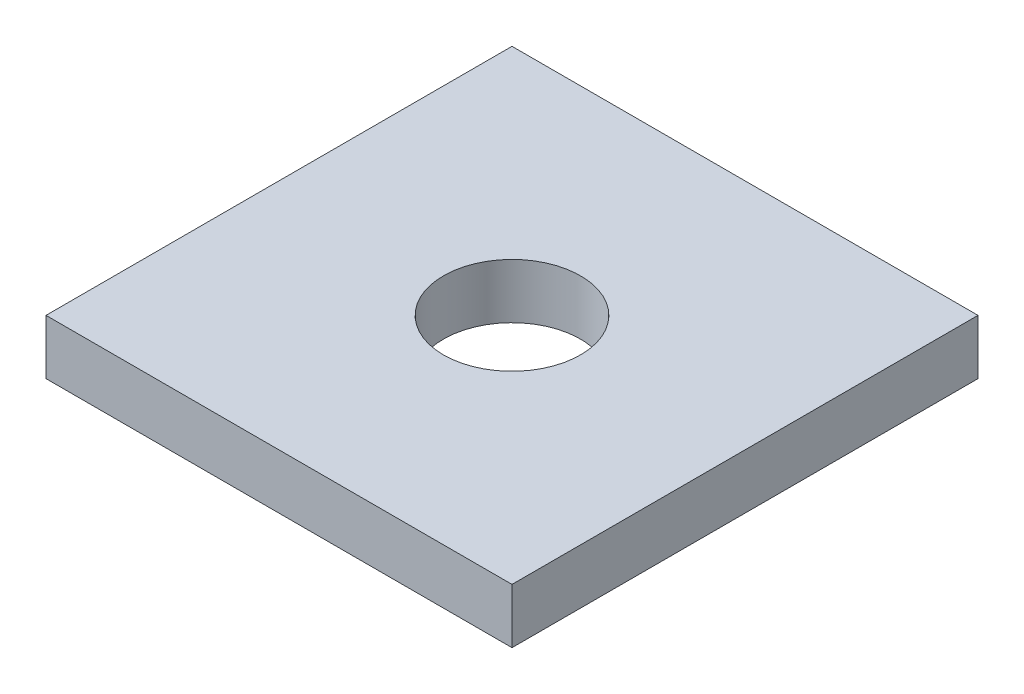
SolidWorks part; units mm, degrees
ref_plane "Front Plane" through (0, 0, 0) normal (0, 0, 1) x (1, 0, 0)
ref_plane "Top Plane" through (0, 0, 0) normal (0, 1, 0) x (1, 0, 0)
ref_plane "Right Plane" through (0, 0, 0) normal (1, 0, 0) x (0, 0, -1)
sketch "Sketch1" plane through (0, 0, 0) normal (0, 1, 0) x (1, 0, 0)
  line L1 (170, 170) -> (-170, 170)
  line L2 (170, 170) -> (170, -170)
  line L3 (170, -170) -> (-170, -170)
  line L4 (-170, 170) -> (-170, -170)
  line L5 (170, 170) -> (-170, -170) construction
  line L6 (170, -170) -> (-170, 170) construction
  point P0 (0, 0)
  dimension "D1" = 340
  dimension "D2" = 340
extrude "Boss-Extrude1" add sketch "Sketch1" along normal blind 40 contours L1 L4 L3 L2
sketch "Sketch2" plane through (0, 40, 0) normal (0, 1, 0) x (1, 0, 0)
  circle A0 centre (0, 0) radius 50
  dimension "D1" = 100
extrude "Cut-Extrude1" cut sketch "Sketch2" against normal blind 40
